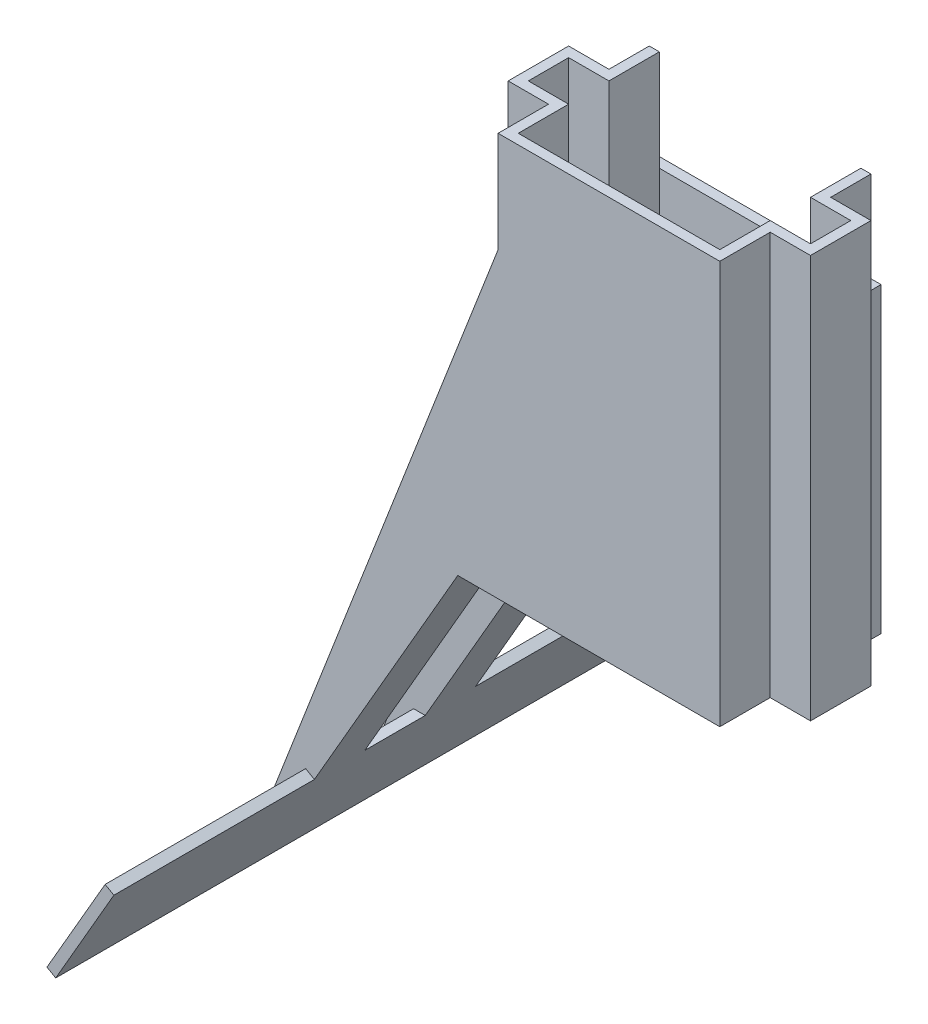
SolidWorks part; units mm, degrees
ref_plane "Ebene vorne" through (0, 0, 0) normal (0, 0, 1) x (1, 0, 0)
ref_plane "Ebene oben" through (0, 0, 0) normal (0, 1, 0) x (1, 0, 0)
ref_plane "Ebene rechts" through (0, 0, 0) normal (1, 0, 0) x (0, 0, -1)
sketch "Skizze1" plane through (0, 0, 0) normal (0, 1, 0) x (1, 0, 0)
  line L0 (2, 2) -> (2, 4.5)
  line L1 (12, -2.5) -> (2, -2.5)
  line L2 (12, -2.5) -> (12, 0)
  line L3 (12, 4.5) -> (2, 4.5)
  line L4 (2, -2.5) -> (2, 0)
  line L5 (1.5, 2.5) -> (1.5, 5)
  line L6 (12.5, 5) -> (1.5, 5)
  line L7 (14, 0) -> (12, 0)
  line L8 (14, 0) -> (14, 2)
  line L9 (14, 2) -> (12, 2)
  line L10 (0, 0) -> (0, 2)
  line L11 (12.5, 2.5) -> (12.5, 5)
  line L12 (14.5, 2.5) -> (12.5, 2.5)
  line L17 (14.5, -0.5) -> (14.5, 2.5)
  line L18 (14.5, -0.5) -> (12.5, -0.5)
  line L19 (2, 2) -> (0, 2)
  line L20 (12, 2) -> (12, 4.5)
  line L21 (2, 0) -> (0, 0)
  line L22 (12.5, -3) -> (12.5, -0.5)
  line L39 (12.5, -3) -> (1.5, -3)
  line L40 (1.5, -3) -> (1.5, -0.5)
  line L41 (1.5, -0.5) -> (-0.5, -0.5)
  line L42 (-0.5, -0.5) -> (-0.5, 2.5)
  line L43 (1.5, 2.5) -> (-0.5, 2.5)
  point P0 (0, 0)
  point P5 (0, 0)
  point P11 (0, 0)
  dimension "D1" = 10
  dimension "D2" = 2
  dimension "D3" = 14
  dimension "D4" = 0.5
  dimension "D6" = 7
extrude "Aufsatz-Linear austragen1" add sketch "Skizze1" along normal blind 20
sketch "Skizze2" plane through (0, 0, -5) normal (0, 0, -1) x (-1, 0, 0)
  line L0 (-1.5, 20) -> (-1.5, 0) construction
  line L1 (-12.5, 20) -> (-1.5, 20)
  line L2 (-12.5, 20) -> (-12.5, 15)
  line L3 (-12.5, 15) -> (-1.5, 15)
  line L4 (-1.5, 20) -> (-1.5, 15)
  dimension "D1" = 5
extrude "Schnitt-Linear austragen1" cut sketch "Skizze2" against normal blind 0.5
sketch "Skizze3" plane through (0, 0, -5) normal (0, 0, -1) x (-1, 0, 0)
  line L0 (-1.5, 0) -> (0.5, 0)
  line L1 (0.5, 0) -> (10.5, -17.3205)
  line L2 (10.5, -17.3205) -> (10.933, -17.0705)
  line L3 (10.933, -17.0705) -> (0.7887, 0.5)
  line L5 (-1.5, 0.5) -> (0.7887, 0.5)
  line L6 (-1.5, 15) -> (-1.5, 0) construction
  line L7 (0.5, 20) -> (0.5, 0) construction
  line L12 (-1.5, 0) -> (-1.5, 15)
  line L13 (-1.5, 15) -> (-12.5, 15)
  line L14 (-12.5, 15) -> (-12.5, 0)
  line L15 (-12.5, 0) -> (-1.5, 0)
  line L16 (-1.5, 0) -> (-1.5, 0.5)
  dimension "D1" = 20
  dimension "D2" = 0.5
  dimension "D3" = 0.5
  dimension "D4" = 150
  dimension "D5" = 0
extrude "Aufsatz-Linear austragen2" add sketch "Skizze3" against normal up to surface (8 mm away) up to face at (7, 10, 3)
sketch "Skizze4" plane through (0, 0.5, 0) normal (0, 1, 0) x (1, 0, 0)
  line L1 (0, 2) -> (1.5, 2)
  line L2 (0, 2) -> (0, 0)
  line L3 (0, 0) -> (1.5, 0)
  line L4 (1.5, 2) -> (1.5, 0)
extrude "Schnitt-Linear austragen2" cut sketch "Skizze4" against normal blind 8
sketch "Skizze6" plane through (0, 0, -5) normal (0, 0, -1) x (-1, 0, 0)
  line L0 (-1.5, 15) -> (10.933, -17.0705)
  line L1 (10.933, -17.0705) -> (0.7887, 0.5)
  line L2 (0.7887, 0.5) -> (-1.5, 0.5)
  line L3 (-1.5, 0.5) -> (-1.5, 15)
extrude "Aufsatz-Linear austragen3" add sketch "Skizze6" against normal up to surface (2.5 mm away) up to face at (0.5, 10.25, -2.5)
ref_plane "Ebene1" through (0, 0, -1) normal (0, 0, -1) x (-1, 0, 0)
sketch "Skizze8" plane through (0, 0, 0) normal (1, 0, 0) x (0, 0, -1)
  line L0 (2.5, 20) -> (2.5, 0) construction
  line L1 (-0.5, 0) -> (2.5, 0)
  line L2 (-0.5, 0) -> (-0.5, -12.3205)
  line L3 (-0.5, -12.3205) -> (2.5, -12.3205)
  line L4 (2.5, 0) -> (2.5, -12.3205)
  line L6 (-3, -17.3205) -> (5, -17.3205) construction
  point P7 (2.45, -12.9915)
  dimension "D1" = 5
extrude "Schnitt-Linear austragen5" cut sketch "Skizze8" against normal blind 12
sketch "Skizze9" plane through (-0.375, 0.2165, 0) normal (0.866, -0.5, 0) x (0, 0, -1)
  line L0 (-0.5, -14.4765) -> (2.5, -14.4765) construction
  line L1 (-3, -20.25) -> (-12.95, -20.25)
  line L2 (-3, -20.25) -> (-3, -14.4765)
  line L3 (-3, -14.4765) -> (-12.95, -14.4765)
  line L4 (-12.95, -20.25) -> (-12.95, -14.4765)
  line L5 (5, -20.25) -> (15, -20.25)
  line L6 (5, -20.25) -> (5, -14.4765)
  line L7 (5, -14.4765) -> (15, -14.4765)
  line L8 (15, -20.25) -> (15, -14.4765)
  point P12 (-2.95, -20.25)
  point P13 (-2.95, -20.25)
  point P14 (-2.95, -14.4765)
  dimension "D1" = 10
extrude "Aufsatz-Linear austragen5" add sketch "Skizze9" against normal blind 0.5
sketch "Skizze11" plane through (0, 0, 0.5) normal (0, 0, 1) x (1, 0, 0)
  line L0 (1.5, 0.5) -> (-0.7887, 0.5)
  line L1 (-0.7887, 0.5) -> (-10.933, -17.0705)
  line L2 (-10.933, -17.0705) -> (1.5, 15)
  line L3 (-10.933, -17.0705) -> (-0.5, 9.8411) construction
  line L4 (1.5, 20) -> (1.5, 0.5) construction
  line L5 (1.5, 15) -> (1.5, 0.5)
extrude "Aufsatz-Linear austragen6" add sketch "Skizze11" along normal up to surface (2.5 mm away) up to face at (1.3815, 2.0761, 3)
